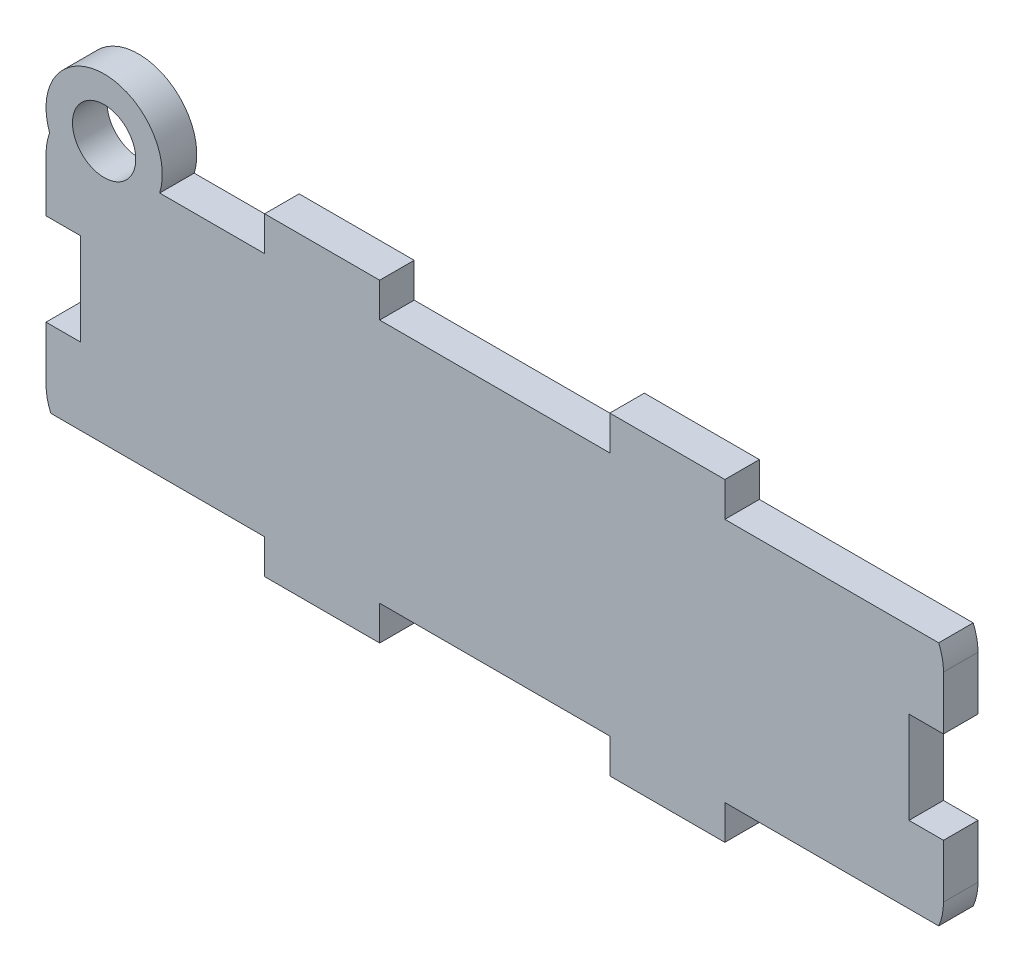
SolidWorks part; units mm, degrees
ref_plane "Front Plane" through (0, 0, 0) normal (0, 0, 1) x (1, 0, 0)
ref_plane "Top Plane" through (0, 0, 0) normal (0, 1, 0) x (1, 0, 0)
ref_plane "Right Plane" through (0, 0, 0) normal (1, 0, 0) x (0, 0, -1)
sketch "Sketch1" plane through (0, 0, 0) normal (0, 0, 1) x (1, 0, 0)
  line L0 (52, -3) -> (52, 0) construction
  line L1 (-7, -3) -> (3, -3)
  line L2 (-26, 2) -> (-26, 19.3118)
  line L3 (-7, 24.3118) -> (3, 24.3118)
  line L4 (52, 2) -> (52, 19.3118)
  line L5 (-26, -3) -> (52, 24.3118) construction
  line L6 (-26, 24.3118) -> (52, -3) construction
  line L7 (23, -3) -> (33, -3)
  line L8 (-7, 0) -> (-25.5826, 0)
  line L9 (-7, 0) -> (-7, -3)
  line L12 (-7, 0) -> (-26, -3) construction
  line L13 (-7, -3) -> (-26, 0) construction
  line L15 (3, -3) -> (3, 0)
  line L16 (3, 0) -> (23, 0)
  line L17 (23, -3) -> (23, 0)
  line L18 (3, -3) -> (23, 0) construction
  line L19 (3, 0) -> (23, -3) construction
  line L21 (33, -3) -> (33, 0)
  line L22 (33, 0) -> (51.5826, 0)
  line L24 (33, -3) -> (52, 0) construction
  line L25 (33, 0) -> (52, -3) construction
  line L27 (-33.6771, 10.6559) -> (59.6771, 10.6559) construction
  line L28 (33, 24.3118) -> (33, 21.3118)
  line L29 (23, 24.3118) -> (33, 24.3118)
  line L30 (23, 24.3118) -> (23, 21.3118)
  line L31 (3, 24.3118) -> (3, 21.3118)
  line L32 (-7, 21.3118) -> (-7, 24.3118)
  line L34 (-7, 21.3118) -> (-25.5826, 21.3118)
  line L35 (3, 21.3118) -> (23, 21.3118)
  line L36 (33, 21.3118) -> (51.5826, 21.3118)
  arc A1 (-26, 19.3118) -> (-25.5826, 21.3118) centre (-21, 19.3118) cw
  arc A2 (51.5826, 21.3118) -> (52, 19.3118) centre (47, 19.3118) cw
  arc A4 (-25.5826, 0) -> (-26, 2) centre (-21, 2) cw
  arc A5 (51.5826, 0) -> (52, 2) centre (47, 2) ccw
  point P4 (13, 10.6559)
  point P24 (-16.5, -1.5)
  point P29 (13, -1.5)
  point P35 (42.5, -1.5)
  point P41 (13, 10.6559)
  point P49 (0, 0)
  point P50 (33, -3)
  point P52 (0, 0)
  point P53 (-7, 0)
extrude "Boss-Extrude1" add sketch "Sketch1" along normal blind 3
sketch "Sketch3" plane through (0, 0, 0) normal (0, 0, -1) x (-1, 0, 0)
  circle A0 centre (20.9461, 22.8118) radius 2.7498 construction
  circle A1 centre (20.9461, 22.8118) radius 2.7498
  arc A2 (25.6856, 21.057) -> (16.1199, 21.3118) centre (20.9461, 22.8118) ccw construction
  arc A3 (25.6856, 21.057) -> (16.1199, 21.3118) centre (20.9461, 22.8118) ccw construction
  circle A4 centre (20.9461, 22.8118) radius 5.0539
extrude "Boss-Extrude3" add sketch "Sketch3" against normal blind 3
sketch "Sketch4" plane through (0, 0, 0) normal (0, 0, -1) x (-1, 0, 0)
  line L0 (23.2507, 21.3118) -> (18.6415, 21.3118)
  arc A2 (18.6415, 21.3118) -> (23.2507, 21.3118) centre (20.9461, 22.8118) ccw
extrude "Cut-Extrude1" cut sketch "Sketch4" against normal blind 3
sketch "Sketch5" plane through (0, 0, 0) normal (0, 0, -1) x (-1, 0, 0)
  line L0 (26, 10.6559) -> (-52, 10.6559) construction
  line L1 (26, 19.3118) -> (26, 2) construction
  line L2 (-52, 2) -> (-52, 19.3118) construction
  line L3 (-13, 0) -> (-13, 21.3118) construction
  line L4 (26, 6.6559) -> (23, 6.6559)
  line L5 (26, 6.6559) -> (26, 14.6559)
  line L6 (26, 14.6559) -> (23, 14.6559)
  line L7 (23, 6.6559) -> (23, 14.6559)
  line L8 (26, 6.6559) -> (23, 14.6559) construction
  line L9 (26, 14.6559) -> (23, 6.6559) construction
  line L10 (-3, 0) -> (-23, 0) construction
  line L11 (-23, 21.3118) -> (-3, 21.3118) construction
  line L12 (-52, 14.6559) -> (-49, 6.6559) construction
  line L13 (-52, 6.6559) -> (-49, 14.6559) construction
  line L14 (-49, 6.6559) -> (-49, 14.6559)
  line L15 (-52, 14.6559) -> (-49, 14.6559)
  line L16 (-52, 6.6559) -> (-52, 14.6559)
  line L17 (-52, 6.6559) -> (-49, 6.6559)
  point P10 (24.5, 10.6559)
  point P21 (-50.5, 10.6559)
  dimension "D1" = 3
  dimension "D2" = 8
extrude "Cut-Extrude2" cut sketch "Sketch5" against normal blind 3
